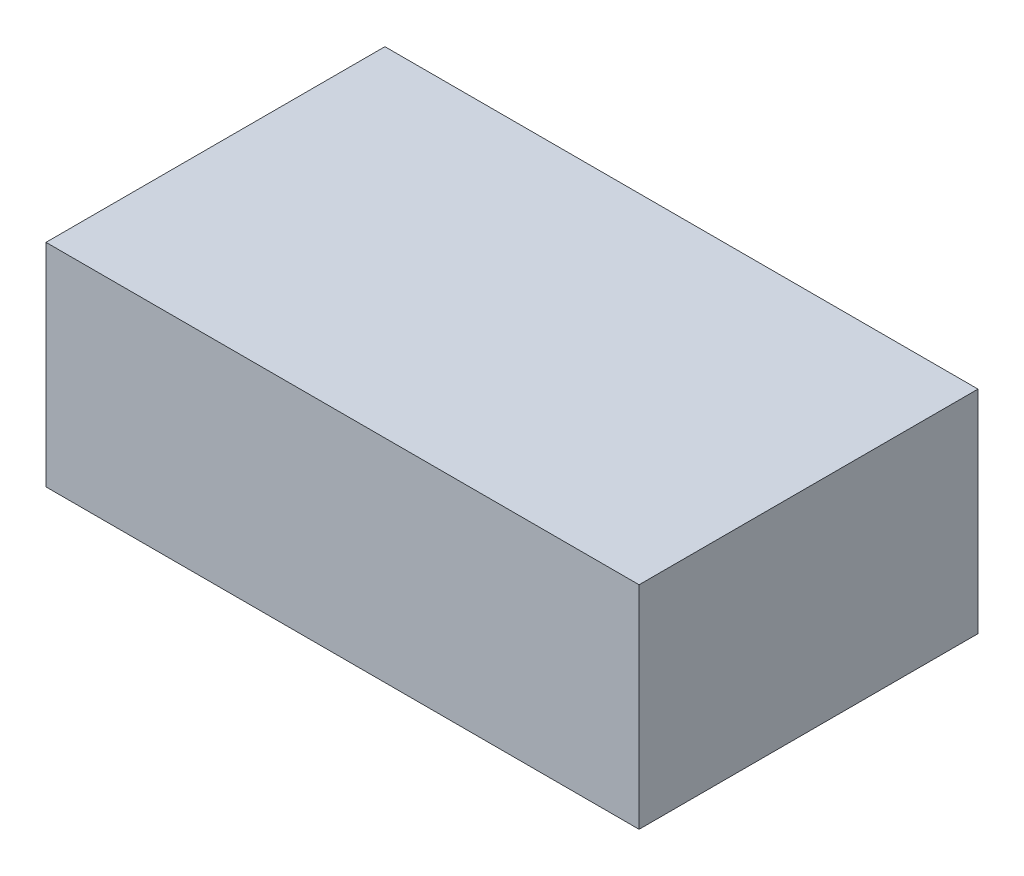
SolidWorks part; units mm, degrees
ref_plane "Front Plane" through (0, 0, 0) normal (0, 0, 1) x (1, 0, 0)
ref_plane "Top Plane" through (0, 0, 0) normal (0, 1, 0) x (1, 0, 0)
ref_plane "Right Plane" through (0, 0, 0) normal (1, 0, 0) x (0, 0, -1)
sketch "Sketch1" plane through (0, 0, 0) normal (0, 0, 1) x (1, 0, 0)
  line L1 (-8.89, 3.175) -> (8.89, 3.175)
  line L2 (-8.89, 3.175) -> (-8.89, -3.175)
  line L3 (-8.89, -3.175) -> (8.89, -3.175)
  line L4 (8.89, 3.175) -> (8.89, -3.175)
  point P4 (0, 3.175)
  point P6 (8.89, 0)
  dimension "D1" = 6.35
  dimension "D2" = 17.78
extrude "Boss-Extrude1" add sketch "Sketch1" along normal blind 10.16
